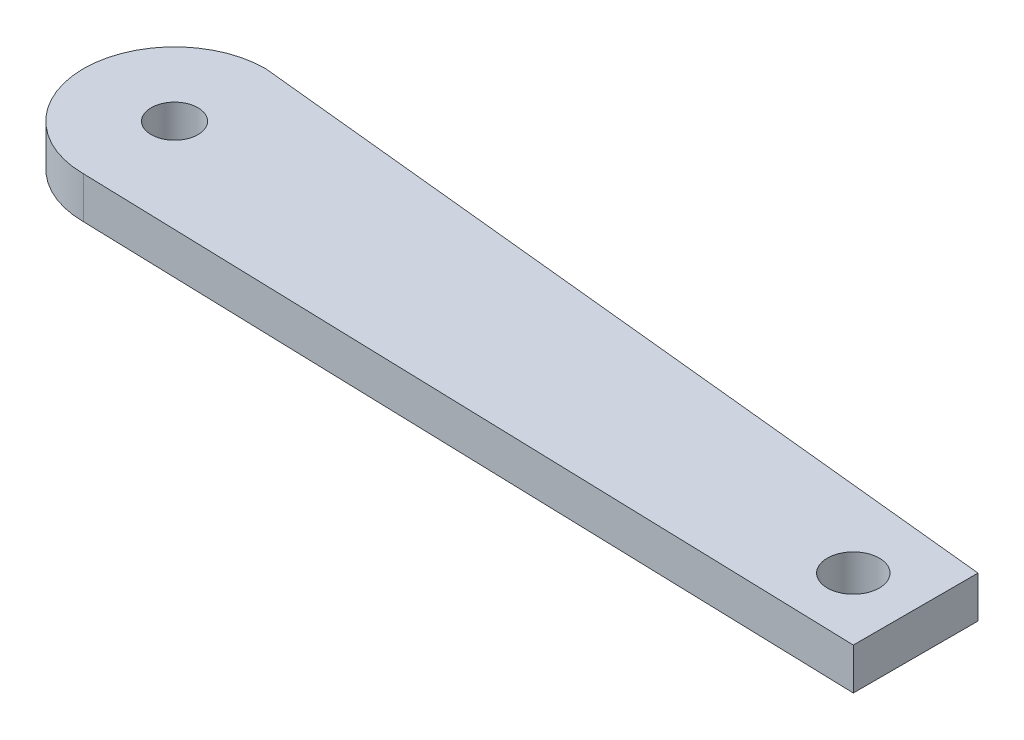
SolidWorks part; units mm, degrees
ref_plane "Front Plane" through (0, 0, 0) normal (0, 0, 1) x (1, 0, 0)
ref_plane "Top Plane" through (0, 0, 0) normal (0, 1, 0) x (1, 0, 0)
ref_plane "Right Plane" through (0, 0, 0) normal (1, 0, 0) x (0, 0, -1)
sketch "Sketch1" plane through (0, 0, 0) normal (0, 1, 0) x (1, 0, 0)
  line L0 (0, 8.7635) -> (76.3225, 1)
  line L1 (76.3225, 1) -> (76.3225, -11)
  line L2 (76.3225, -11) -> (0, -8.7635)
  circle A0 centre (0, 0) radius 2.25
  circle A1 centre (70.3225, -5) radius 2.5
  arc A2 (1.7646, 8.584) -> (0, -8.7635) centre (0, 0) ccw
  dimension "D1" = 4.5
  dimension "D2" = 5
  dimension "D3" = 70.5
  dimension "D4" = 5
  dimension "D5" = 6
  dimension "D6" = 6
  dimension "D7" = 6
extrude "Boss-Extrude1" add sketch "Sketch1" along normal blind 4 contours L0 A2 L2 L1 A0 A1
